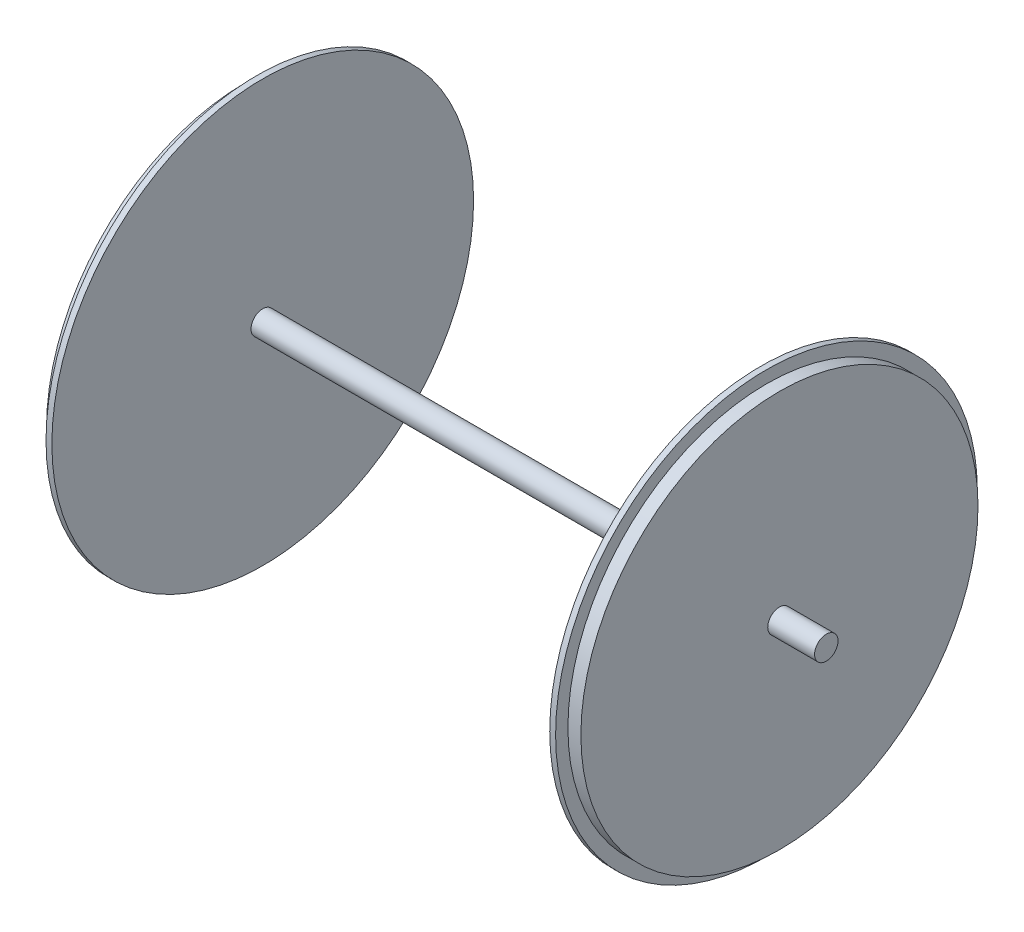
SolidWorks part; units mm, degrees
ref_plane "Front Plane" through (0, 0, 0) normal (0, 0, 1) x (1, 0, 0)
ref_plane "Top Plane" through (0, 0, 0) normal (0, 1, 0) x (1, 0, 0)
ref_plane "Right Plane" through (0, 0, 0) normal (1, 0, 0) x (0, 0, -1)
sketch "Sketch1" plane through (0, 0, 0) normal (0, 0, 1) x (1, 0, 0)
  line L0 (-2977.3154, 50.8) -> (-818.3154, 50.8)
  line L1 (-3053.5154, 0) -> (-736.6, 0)
  line L2 (-792.9154, 914.4) -> (-818.3154, 914.4)
  line L3 (-818.3154, 914.4) -> (-818.3154, 50.8)
  line L4 (-3053.5154, 50.8) -> (-3053.5154, 861.0115)
  line L5 (-3002.7154, 914.4) -> (-2977.3154, 914.4)
  line L6 (-2977.3154, 914.4) -> (-2977.3154, 50.8)
  line L7 (-736.6, 50.8) -> (-736.6, 861.0115)
  line L8 (-3002.7154, 914.4) -> (-3002.7154, 861.0115)
  line L9 (-3002.7154, 861.0115) -> (-3053.5154, 861.0115)
  line L10 (-736.6, 861.0115) -> (-792.9154, 861.0115)
  line L11 (-792.9154, 861.0115) -> (-792.9154, 914.4)
  line L12 (-3053.5154, 0) -> (-3256.7154, 0)
  line L13 (-736.6, 0) -> (-533.4, 0)
  line L14 (-533.4, 0) -> (-533.4, 50.8)
  line L15 (-533.4, 50.8) -> (-736.6, 50.8)
  line L16 (-3256.7154, 0) -> (-3256.7154, 50.8)
  line L17 (-3256.7154, 50.8) -> (-3053.5154, 50.8)
  dimension "D1" = 50.8
  dimension "D2" = 25.4
  dimension "D3" = 2159
revolve "Revolve2" add sketch "Sketch1" angle 360 about L1
